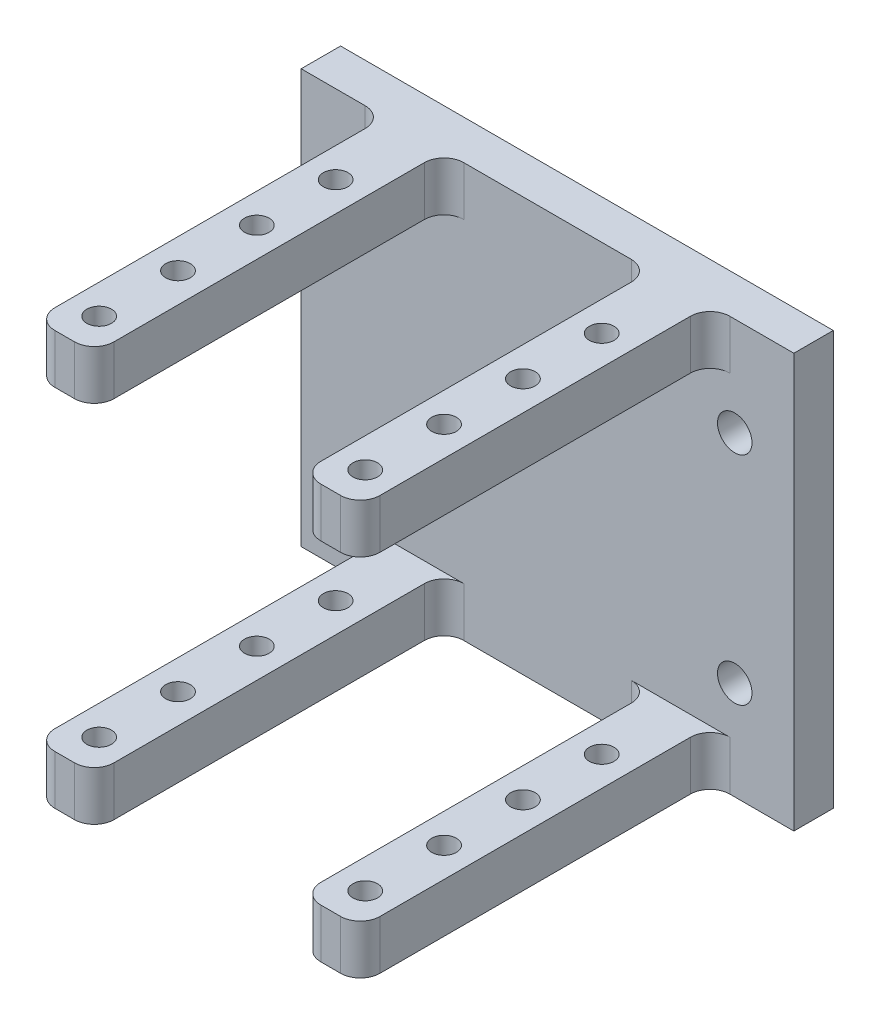
SolidWorks part; units mm, degrees
ref_plane "Plan de face" through (0, 0, 0) normal (0, 0, 1) x (1, 0, 0)
ref_plane "Plan de dessus" through (0, 0, 0) normal (0, 1, 0) x (1, 0, 0)
ref_plane "Plan de droite" through (0, 0, 0) normal (1, 0, 0) x (0, 0, -1)
sketch "Esquisse1" plane through (0, 0, 0) normal (0, 0, 1) x (1, 0, 0)
  line L1 (-25, -21) -> (25, -21)
  line L2 (-25, -21) -> (-25, 21)
  line L3 (-25, 21) -> (25, 21)
  line L4 (25, -21) -> (25, 21)
  line L5 (-25, -21) -> (25, 21) construction
  line L6 (-25, 21) -> (25, -21) construction
  line L7 (19, -11) -> (-19, -11) construction
  line L8 (19, -11) -> (19, 11) construction
  line L9 (19, 11) -> (-19, 11) construction
  line L10 (-19, -11) -> (-19, 11) construction
  line L11 (19, -11) -> (-19, 11) construction
  line L12 (19, 11) -> (-19, -11) construction
  circle A0 centre (-19, 11) radius 1.75
  circle A1 centre (19, 11) radius 1.75
  circle A2 centre (19, -11) radius 1.75
  circle A3 centre (-19, -11) radius 1.75
  point P0 (0, 0)
  point P6 (0, 0)
extrude "Boss.-Extru.1" add sketch "Esquisse1" along normal blind 4
sketch "Esquisse2" plane through (0, 0, 4) normal (0, 0, 1) x (1, 0, 0)
  line L0 (25, 21) -> (-25, 21) construction
  line L1 (-16.5, 21) -> (-10.5, 21)
  line L2 (-16.5, 21) -> (-16.5, 16)
  line L3 (-16.5, 16) -> (-10.5, 16)
  line L4 (-10.5, 21) -> (-10.5, 16)
  line L5 (-10.5, 21) -> (0, 21) construction
  line L6 (16.5, 21) -> (10.5, 21)
  line L7 (16.5, 21) -> (16.5, 16)
  line L8 (16.5, 16) -> (10.5, 16)
  line L9 (10.5, 21) -> (10.5, 16)
  line L10 (0, 21) -> (10.5, 21) construction
  line L11 (0, 21) -> (0, 0) construction
  line L12 (0, 0) -> (4.2364, 0) construction
  line L13 (-16.5, -21) -> (-16.5, -16)
  line L14 (-16.5, -21) -> (-10.5, -21)
  line L15 (-10.5, -21) -> (-10.5, -16)
  line L16 (-16.5, -16) -> (-10.5, -16)
  line L17 (16.5, -21) -> (16.5, -16)
  line L18 (16.5, -21) -> (10.5, -21)
  line L19 (10.5, -21) -> (10.5, -16)
  line L20 (16.5, -16) -> (10.5, -16)
extrude "Boss.-Extru.2" add sketch "Esquisse2" along normal blind 35.5
sketch "Esquisse3" plane through (0, 21, 0) normal (0, 1, 0) x (1, 0, 0)
  line L0 (-13.5, -39.5) -> (-13.5, -4) construction
  line L1 (-10.5, -39.5) -> (-16.5, -39.5) construction
  line L2 (10.5, -4) -> (-10.5, -4) construction
  line L3 (0, 0) -> (0, -7.3093) construction
  line L4 (25, 0) -> (-25, 0) construction
  circle A0 centre (-13.5, -12) radius 1.25
  circle A1 centre (-13.5, -20) radius 1.25
  circle A2 centre (-13.5, -28) radius 1.25
  circle A3 centre (-13.5, -36) radius 1.25
  circle A4 centre (13.5, -36) radius 1.25
  circle A5 centre (13.5, -28) radius 1.25
  circle A6 centre (13.5, -20) radius 1.25
  circle A7 centre (13.5, -12) radius 1.25
extrude "Enlèv. mat.-Extru.1" cut sketch "Esquisse3" against normal through all
fillet "Congé1" radius 2 16 edges at (-16.5, -18.5, 39.5) (-16.5, 18.5, 39.5) (16.5, -18.5, 39.5) (16.5, 18.5, 39.5) (10.5, -18.5, 4) (16.5, -18.5, 4) (-10.5, -18.5, 4) (-16.5, -18.5, 4) (-16.5, 18.5, 4) (-10.5, 18.5, 4) (10.5, 18.5, 4) (16.5, 18.5, 4) (-10.5, -18.5, 39.5) (10.5, -18.5, 39.5) (10.5, 18.5, 39.5) (-10.5, 18.5, 39.5)
